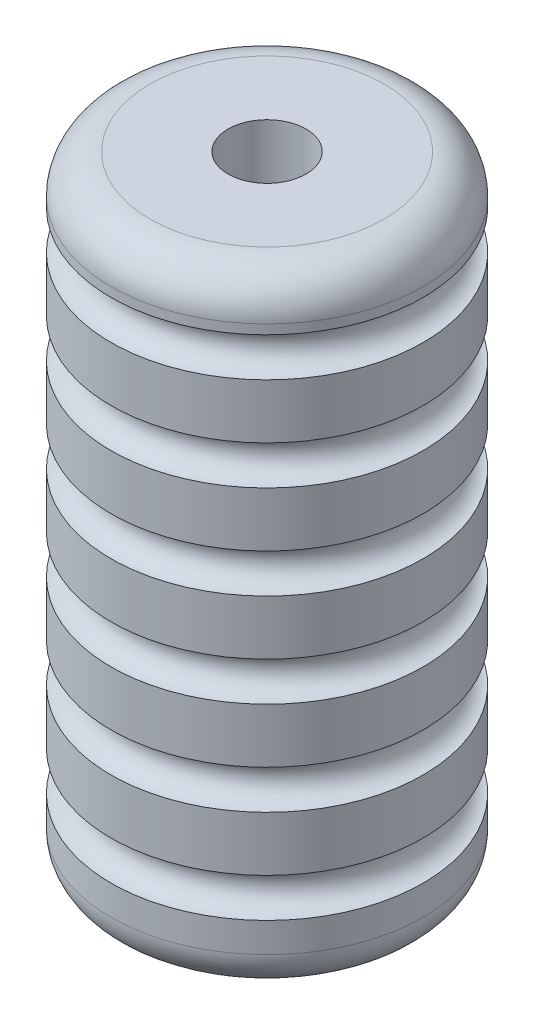
SolidWorks part; units mm, degrees
ref_plane "Front" through (0, 0, 0) normal (0, 0, 1) x (1, 0, 0)
ref_plane "Top" through (0, 0, 0) normal (0, 1, 0) x (1, 0, 0)
ref_plane "Right" through (0, 0, 0) normal (1, 0, 0) x (0, 0, -1)
sketch "Sketch2" plane through (0, 0, 0) normal (1, 0, 0) x (0, 0, -1)
  line L0 (25.4, 93.7227) -> (25.4, 95.25)
  line L1 (0, 0) -> (19.05, 0)
  line L2 (0, 0) -> (0, 101.6)
  line L3 (0, 101.6) -> (19.05, 101.6)
  line L4 (25.4, 6.35) -> (25.4, 11.1727)
  line L5 (25.4, 78.4827) -> (25.4, 87.3727)
  line L6 (25.4, 63.2427) -> (25.4, 72.1327)
  line L7 (25.4, 48.0027) -> (25.4, 56.8927)
  line L8 (25.4, 32.7627) -> (25.4, 41.6527)
  line L9 (25.4, 17.5227) -> (25.4, 26.4127)
  arc A0 (25.4, 93.7227) -> (25.4, 87.3727) centre (25.4, 90.5477) ccw
  arc A1 (25.4, 78.4827) -> (25.4, 72.1327) centre (25.4, 75.3077) ccw
  arc A2 (25.4, 63.2427) -> (25.4, 56.8927) centre (25.4, 60.0677) ccw
  arc A3 (25.4, 48.0027) -> (25.4, 41.6527) centre (25.4, 44.8277) ccw
  arc A4 (25.4, 32.7627) -> (25.4, 26.4127) centre (25.4, 29.5877) ccw
  arc A5 (25.4, 17.5227) -> (25.4, 11.1727) centre (25.4, 14.3477) ccw
  arc A6 (19.05, 0) -> (25.4, 6.35) centre (19.05, 6.35) ccw
  arc A7 (19.05, 101.6) -> (25.4, 95.25) centre (19.05, 95.25) cw
  point P4 (12.7, 50.8)
  point P26 (25.4, 0)
  dimension "D3" = 6.35
  dimension "D5" = 6.35
  dimension "D1" = 101.6
  dimension "D2" = 25.4
  dimension "D4" = 6
revolve "Revolve1" add sketch "Sketch2" angle 360 about L2
sketch "Sketch3" plane through (0, 101.6, 0) normal (0, 1, 0) x (1, 0, 0)
  circle A0 centre (0, 0) radius 6.35
  dimension "D1" = 12.7
extrude "Cut-Extrude1" cut sketch "Sketch3" against normal through all
